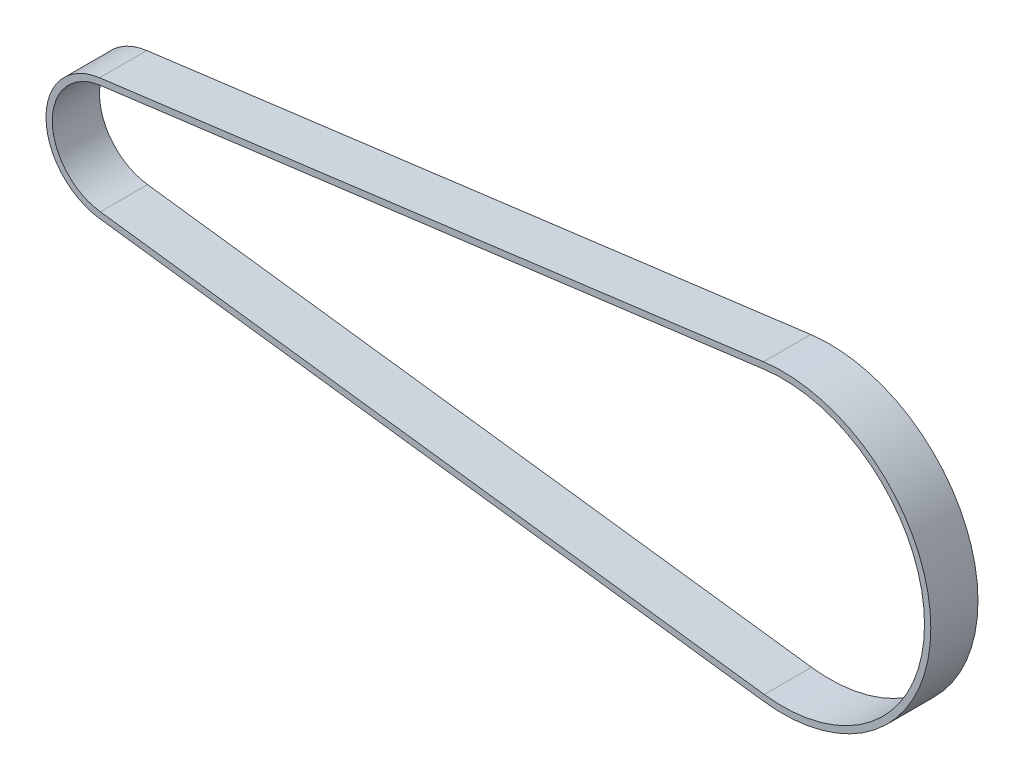
SolidWorks part; units mm, degrees
ref_plane "Front" through (0, 0, 0) normal (0, 0, 1) x (1, 0, 0)
ref_plane "Top" through (0, 0, 0) normal (0, 1, 0) x (1, 0, 0)
ref_plane "Right" through (0, 0, 0) normal (1, 0, 0) x (0, 0, -1)
sketch "Sketch1" plane through (0, 0, 0) normal (0, 0, 1) x (1, 0, 0)
  line L0 (-2.864, 22.1024) -> (265.1774, 56.8349)
  line L1 (265.1774, -56.8349) -> (-2.864, -22.1024)
  line L2 (0, 0) -> (272.542, 0) construction
  arc A0 (-2.864, 22.1024) -> (-2.864, -22.1024) centre (0, 0) ccw
  arc A1 (265.1774, 56.8349) -> (265.1774, -56.8349) centre (272.542, 0) cw
  dimension "D1" = 57.31
  dimension "D2" = 22.2872
  dimension "D3" = 272.542
extrude "Extrude-Thin1" add sketch "Sketch1" along normal blind 9.525 and the other way blind 9.525 thin thin type one direction wall 2.54
